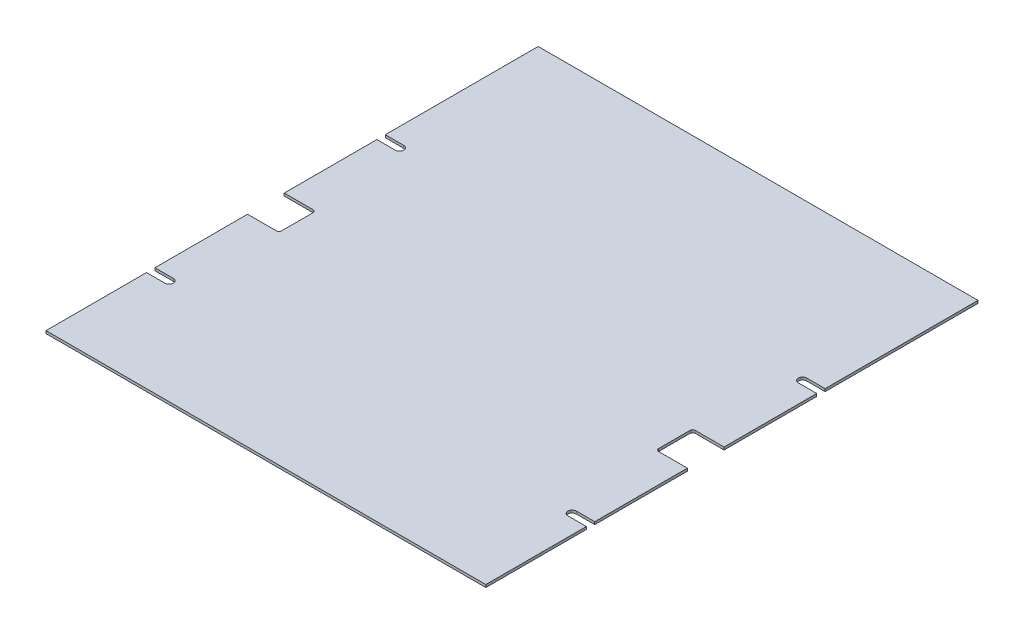
SolidWorks part; units mm, degrees
material "PC High Viscosity"
ref_plane "Front Plane" through (0, 0, 0) normal (0, 0, 1) x (1, 0, 0)
ref_plane "Top Plane" through (0, 0, 0) normal (0, 1, 0) x (1, 0, 0)
ref_plane "Right Plane" through (0, 0, 0) normal (1, 0, 0) x (0, 0, -1)
sketch "Sketch1" plane through (0, 0, 0) normal (0, 1, 0) x (1, 0, 0)
  line L1 (-266.7, -298.45) -> (266.7, -298.45)
  line L2 (-266.7, -298.45) -> (-266.7, 298.45)
  line L3 (-266.7, 298.45) -> (266.7, 298.45)
  line L4 (266.7, -298.45) -> (266.7, 298.45)
  line L5 (-266.7, -298.45) -> (266.7, 298.45) construction
  line L6 (-266.7, 298.45) -> (266.7, -298.45) construction
  point P0 (0, 0)
  dimension "D1" = 533.4
  dimension "D2" = 596.9
extrude "Boss-Extrude1" add sketch "Sketch1" along normal blind 3.175
sketch "Sketch5" plane through (0, 0, 0) normal (0, -1, 0) x (1, 0, 0)
  line L0 (247.65, -111.2139) -> (247.65, -85.7758) construction
  line L1 (244.3858, -101.8782) -> (244.3858, -107.9506)
  line L2 (247.65, 168.1861) -> (247.65, 193.6242) construction
  line L3 (250.9136, -101.8783) -> (250.9136, -107.95)
  line L4 (0, -298.45) -> (0, 298.45) construction
  line L5 (266.7, -298.45) -> (-266.7, -298.45) construction
  line L6 (-266.7, 298.45) -> (266.7, 298.45) construction
  line L13 (250.9139, 177.5218) -> (250.9139, 171.45)
  line L15 (244.3861, 177.5218) -> (244.3861, 171.45)
  line L16 (-247.65, 168.1861) -> (-247.65, 193.6242) construction
  line L17 (-247.65, -111.2139) -> (-247.65, -85.7758) construction
  line L18 (-244.3861, 177.5218) -> (-244.3861, 171.45)
  line L19 (-250.9139, 177.5218) -> (-250.9139, 171.45)
  line L20 (-250.9136, -101.8783) -> (-250.9136, -107.95)
  line L21 (-244.3858, -101.8782) -> (-244.3858, -107.9506)
  line L22 (247.65, 298.45) -> (247.65, -298.45) construction
  line L23 (-266.7, 298.45) -> (266.7, 298.45) construction
  line L24 (266.7, -298.45) -> (-266.7, -298.45) construction
  arc A0 (-244.3861, 171.45) -> (-250.9139, 171.45) centre (-247.65, 171.45) cw
  arc A1 (-250.9139, 177.5218) -> (-244.3861, 177.5218) centre (-247.65, 185.2422) cw
  arc A2 (250.9136, -101.8783) -> (244.3858, -101.8782) centre (247.6498, -94.1578) ccw
  arc A3 (-244.3858, -107.9506) -> (-250.9136, -107.95) centre (-247.6497, -107.95) cw
  arc A4 (244.3858, -107.9506) -> (250.9136, -107.95) centre (247.6497, -107.95) ccw
  arc A5 (-250.9136, -101.8783) -> (-244.3858, -101.8782) centre (-247.6498, -94.1578) cw
  arc A6 (250.9139, 177.5218) -> (244.3861, 177.5218) centre (247.65, 185.2422) ccw
  arc A8 (244.3861, 171.45) -> (250.9139, 171.45) centre (247.65, 171.45) ccw
  dimension "D1" = 8.382
  dimension "D2" = 113.2078
  dimension "D4" = 247.65
  dimension "D5" = 6.5278
  dimension "D7" = 3.2639
  dimension "D3" = 25.4381
  dimension "D6" = 190.5
  dimension "D8" = 6.5278
  dimension "D9" = 9.3357
  dimension "D10" = 9.3357
extrude "Cut-Extrude1" [suppressed] cut sketch "Sketch5" against normal through all
hole_wizard "F (0.257) Diameter Slot1" [suppressed] positions "Sketch6" profile "Sketch7" size "F" standard "ANSI Inch"
sketch "Sketch6" plane through (0, 0, 0) normal (0, -1, 0) x (-1, 0, 0)
  line L0 (255.5875, -168.1861) -> (239.7125, -168.1861) construction
  line L1 (255.5875, -171.45) -> (239.7125, -171.45) construction
  point P7 (247.65, -171.45)
  point P12 (247.6497, 107.95)
  point P15 (-247.6497, 107.95)
  point P18 (-247.65, -171.45)
  dimension "D1" = 15.875
  dimension "D2" = 15.875
sketch "Sketch7" plane through (247.65, 0, 171.45) normal (1, 0, 0) x (0, 0, -1)
  line L0 (0, 0) -> (0, 3.175)
  line L1 (0, 3.175) -> (3.2639, 3.175)
  line L2 (3.2639, 3.175) -> (3.2639, 0)
  line L5 (3.2639, 0) -> (0, 0)
  line L11 (0, -6.35) -> (0, 107.95) construction
  dimension "Thru Hole Dia." = 6.5278
  dimension "Thru Hole Depth" = 3.175
sketch "Sketch8" plane through (0, 0, 0) normal (0, -1, 0) x (1, 0, 0)
  line L1 (0, 298.45) -> (0, -298.45) construction
  line L2 (-266.7, -298.45) -> (-266.7, 298.45) construction
  line L3 (-228.6, 53.975) -> (-266.7, 53.975)
  line L4 (-228.6, 53.975) -> (-228.6, 9.525)
  line L5 (-228.6, 9.525) -> (-266.7, 9.525)
  line L6 (-266.7, 53.975) -> (-266.7, 9.525)
  line L7 (-228.6, 53.975) -> (-266.7, 9.525) construction
  line L8 (-228.6, 9.525) -> (-266.7, 53.975) construction
  line L14 (-266.7, 298.45) -> (266.7, 298.45) construction
  line L15 (228.6, 9.525) -> (266.7, 53.975) construction
  line L16 (228.6, 53.975) -> (266.7, 9.525) construction
  line L17 (254.0001, 171.45) -> (252.4122, -107.95) construction
  line L18 (266.7, 53.975) -> (266.7, 9.525)
  line L19 (228.6, 9.525) -> (266.7, 9.525)
  line L20 (228.6, 53.975) -> (228.6, 9.525)
  line L21 (228.6, 53.975) -> (266.7, 53.975)
  point P10 (-247.65, 31.75)
  point P12 (-247.65, 31.75)
  point P26 (247.65, 31.75)
  dimension "D1" = 44.45
  dimension "D2" = 38.1
  dimension "D3" = 266.7
extrude "Cut-Extrude2" cut sketch "Sketch8" against normal through all
fillet "Fillet1" radius 3.175 4 edges at (-228.6, 1.5875, 53.975) (-228.6, 1.5875, 9.525) (228.6, 1.5875, 53.975) (228.6, 1.5875, 9.525)
sketch "Sketch9" plane through (0, 0, 0) normal (0, -1, 0) x (1, 0, 0)
  line L0 (-244.3861, 171.45) -> (-266.7, 171.45) construction
  line L1 (-266.7, 53.975) -> (-266.7, 298.45) construction
  line L2 (-266.7, 171.45) -> (-244.3861, 171.45) construction
  line L3 (-266.7, 176.53) -> (-244.3861, 176.53)
  line L4 (-266.7, 166.37) -> (-244.3861, 166.37)
  line L6 (0, 298.45) -> (0, -298.45) construction
  line L7 (-266.7, 298.45) -> (266.7, 298.45) construction
  line L8 (-228.6, 31.75) -> (228.6, 31.75) construction
  line L10 (-228.6, 12.7) -> (-228.6, 50.8) construction
  line L11 (228.6, 50.8) -> (228.6, 12.7) construction
  line L12 (-244.3861, -107.95) -> (-266.7, -107.95) construction
  line L13 (-266.7, -107.95) -> (-244.3861, -107.95) construction
  line L14 (-266.7, -113.03) -> (-244.3861, -113.03)
  line L15 (-266.7, -102.87) -> (-244.3861, -102.87)
  line L16 (266.7, 171.45) -> (244.3861, 171.45) construction
  line L17 (266.7, 176.53) -> (244.3861, 176.53)
  line L18 (266.7, 166.37) -> (244.3861, 166.37)
  line L19 (266.7, -107.95) -> (244.3861, -107.95) construction
  line L20 (266.7, -113.03) -> (244.3861, -113.03)
  line L21 (266.7, -102.87) -> (244.3861, -102.87)
  line L22 (244.3861, -107.95) -> (266.7, -107.95) construction
  line L23 (244.3861, 171.45) -> (266.7, 171.45) construction
  arc A0 (-266.7, 176.53) -> (-266.7, 166.37) centre (-266.7, 171.45) ccw
  arc A1 (-244.3861, 166.37) -> (-244.3861, 176.53) centre (-244.3861, 171.45) ccw
  arc A2 (-266.7, -113.03) -> (-266.7, -102.87) centre (-266.7, -107.95) cw
  arc A3 (-244.3861, -102.87) -> (-244.3861, -113.03) centre (-244.3861, -107.95) cw
  arc A4 (266.7, 176.53) -> (266.7, 166.37) centre (266.7, 171.45) cw
  arc A5 (244.3861, 166.37) -> (244.3861, 176.53) centre (244.3861, 171.45) cw
  arc A6 (266.7, -113.03) -> (266.7, -102.87) centre (266.7, -107.95) ccw
  arc A7 (244.3861, -102.87) -> (244.3861, -113.03) centre (244.3861, -107.95) ccw
  point P5 (-255.5431, 171.45)
  point P24 (-255.5431, -107.95)
  point P31 (255.5431, 171.45)
  point P38 (255.5431, -107.95)
  dimension "D1" = 5.08
extrude "Cut-Extrude3" cut sketch "Sketch9" against normal through all
